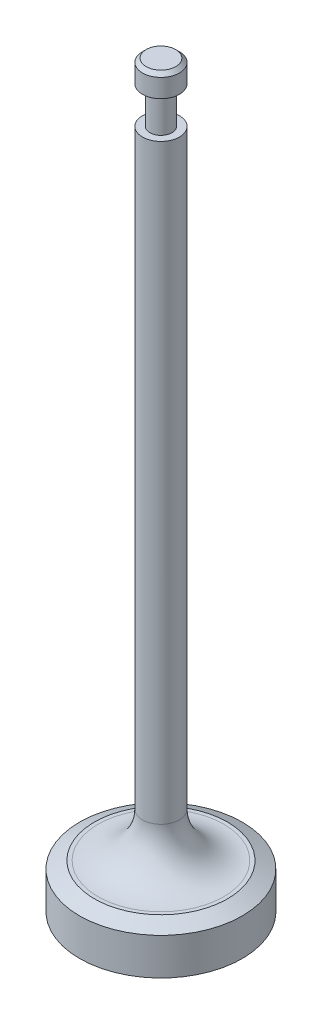
SolidWorks part; units mm, degrees
ref_plane "Front Plane" through (0, 0, 0) normal (0, 0, 1) x (1, 0, 0)
ref_plane "Top Plane" through (0, 0, 0) normal (0, 1, 0) x (1, 0, 0)
ref_plane "Right Plane" through (0, 0, 0) normal (1, 0, 0) x (0, 0, -1)
sketch "Sketch1" plane through (0, 0, 0) normal (1, 0, 0) x (0, 0, -1)
  line L0 (0, 0) -> (0, -100)
  line L1 (0, -100) -> (11, -100)
  line L2 (11, -100) -> (11, -94)
  line L3 (11, -94) -> (2.5, -94)
  line L4 (2.5, -94) -> (2.5, -8)
  line L5 (2.5, -8) -> (1.5, -8)
  line L6 (1.5, -8) -> (1.5, -3)
  line L7 (1.5, -3) -> (2.5, -3)
  line L8 (2.5, -3) -> (2.5, 0)
  line L9 (2.5, 0) -> (0, 0)
  point P3 (11, -97)
  dimension "D1" = 100
  dimension "D2" = 11
  dimension "D3" = 3
  dimension "D4" = 2.5
  dimension "D5" = 3
  dimension "D6" = 5
  dimension "D7" = 1
  dimension "D8" = 2.5
revolve "Revolve1" add sketch "Sketch1" angle 360 about L0
fillet "Fillet1" radius 6 1 edges at (0, -94, 2.5)
chamfer "Chamfer1" distance 1 distance2 2 1 edges at (0, -94, 11)
chamfer "Chamfer3" distance 0.5 angle 45 1 edges at (0, 0, 2.5)
